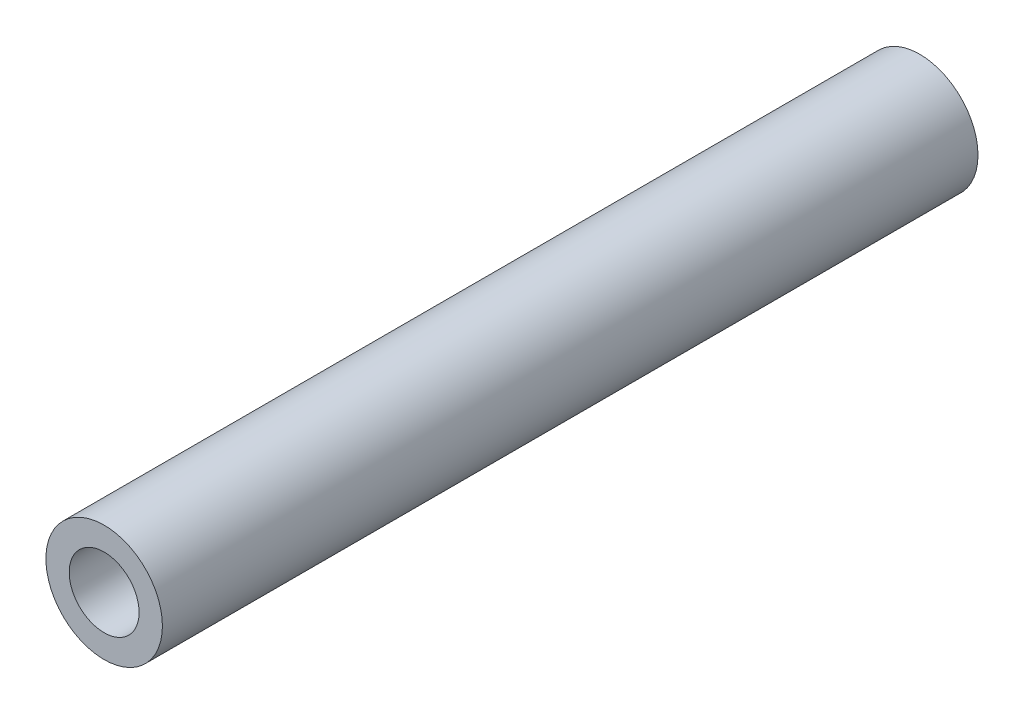
SolidWorks part; units mm, degrees
ref_plane "Front" through (0, 0, 0) normal (0, 0, 1) x (1, 0, 0)
ref_plane "Top" through (0, 0, 0) normal (0, 1, 0) x (1, 0, 0)
ref_plane "Right" through (0, 0, 0) normal (1, 0, 0) x (0, 0, -1)
sketch "Sketch1" plane through (0, 0, 0) normal (0, 0, 1) x (1, 0, 0)
  circle A0 centre (0, 0) radius 1.5
  circle A1 centre (0, 0) radius 2.5
extrude "Boss-Extrude2" add sketch "Sketch1" along normal blind 35
